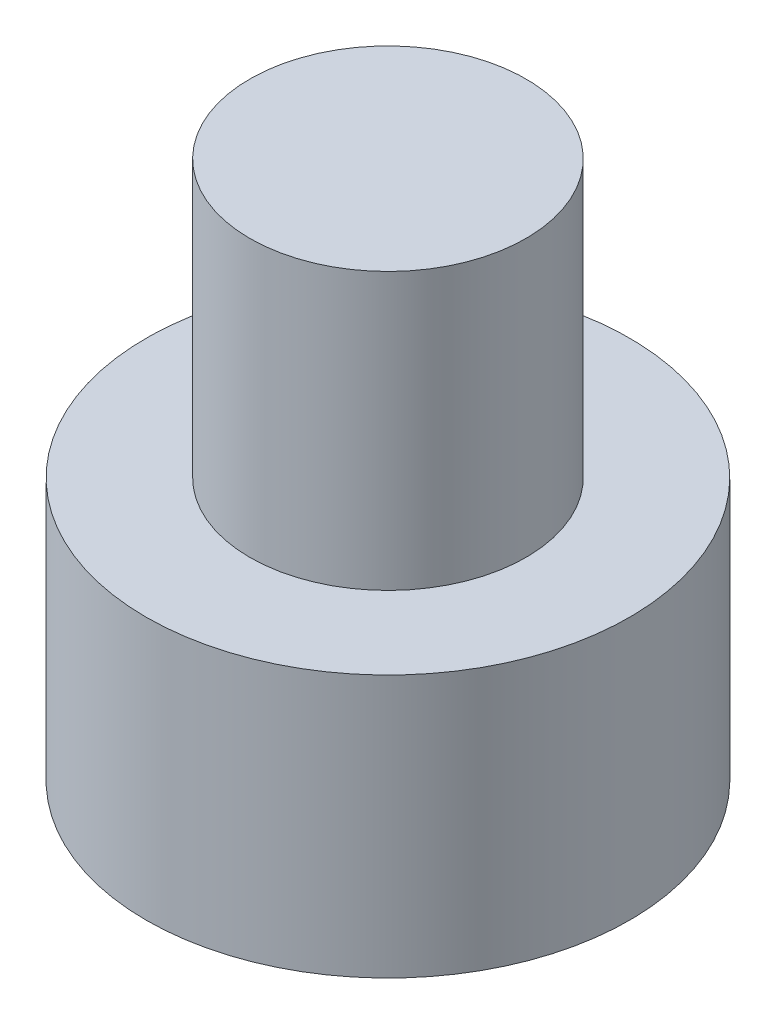
SolidWorks part; units mm, degrees
ref_plane "Front Plane" through (0, 0, 0) normal (0, 0, 1) x (1, 0, 0)
ref_plane "Top Plane" through (0, 0, 0) normal (0, 1, 0) x (1, 0, 0)
ref_plane "Right Plane" through (0, 0, 0) normal (1, 0, 0) x (0, 0, -1)
sketch "Esquisse1" plane through (0, 0, 0) normal (0, 0, 1) x (1, 0, 0)
  line L0 (0, 3.9) -> (0, -3.9) construction
  line L1 (0, -3.9) -> (3.5, -3.9)
  line L2 (3.5, -3.9) -> (3.5, -0.1)
  line L3 (3.5, -0.1) -> (2, -0.1)
  line L4 (2, -0.1) -> (2, 3.9)
  line L5 (2, 3.9) -> (0, 3.9)
  line L6 (0, 3.9) -> (0, -3.9)
  dimension "D1" = 3.8
  dimension "D2" = 4
  dimension "D3" = 3.5
  dimension "D4" = 2
revolve "Révolution1" add sketch "Esquisse1" angle 360 about L0
